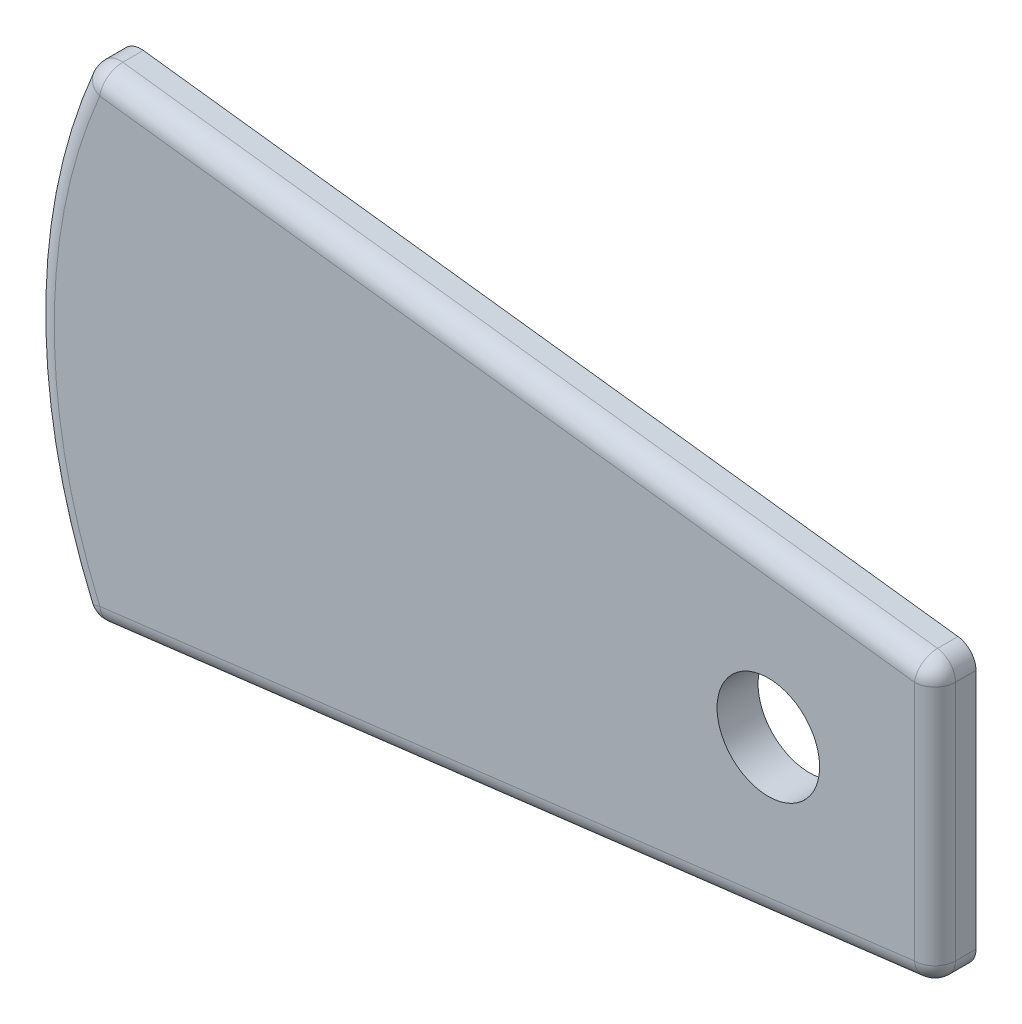
SolidWorks part; units mm, degrees
ref_plane "Front Plane" through (0, 0, 0) normal (0, 0, 1) x (1, 0, 0)
ref_plane "Top Plane" through (0, 0, 0) normal (0, 1, 0) x (1, 0, 0)
ref_plane "Right Plane" through (0, 0, 0) normal (1, 0, 0) x (0, 0, -1)
sketch "Sketch1" plane through (0, 0, 0) normal (0, 0, 1) x (1, 0, 0)
  line L4 (-31.8739, 46.769) -> (-31.8739, 33.231)
  line L5 (-31.8739, 33.231) -> (-73.2085, 28.1457)
  line L6 (-31.8739, 40) -> (-69.6879, 40) construction
  line L7 (-31.8739, 46.769) -> (-73.2085, 51.8543)
  arc A2 (-73.2085, 28.1457) -> (-73.2085, 51.8543) centre (-47.5935, 40) cw
  dimension "D1" = 6.769
extrude "Boss-Extrude1" add sketch "Sketch1" along normal blind 2
fillet "Fillet1" radius 1 4 edges at (-73.2085, 28.1457, 1) (-73.2085, 51.8543, 1) (-31.8739, 46.769, 1) (-31.8739, 33.231, 1)
fillet "Fillet2" radius 1 8 edges at (-73.0946, 51.639, 2) (-52.6133, 49.3205, 2) (-32.1248, 46.547, 2) (-31.8739, 40, 2) (-32.1248, 33.453, 2) (-52.6133, 30.6795, 2) (-73.0946, 28.361, 2) (-75.8185, 40, 2)
sketch "Sketch2" plane through (0, 0, 2) normal (0, 0, 1) x (1, 0, 0)
  circle A0 centre (-40, 40) radius 2.5
  dimension "D1" = 5
extrude "Cut-Extrude2" cut sketch "Sketch2" against normal blind 2
